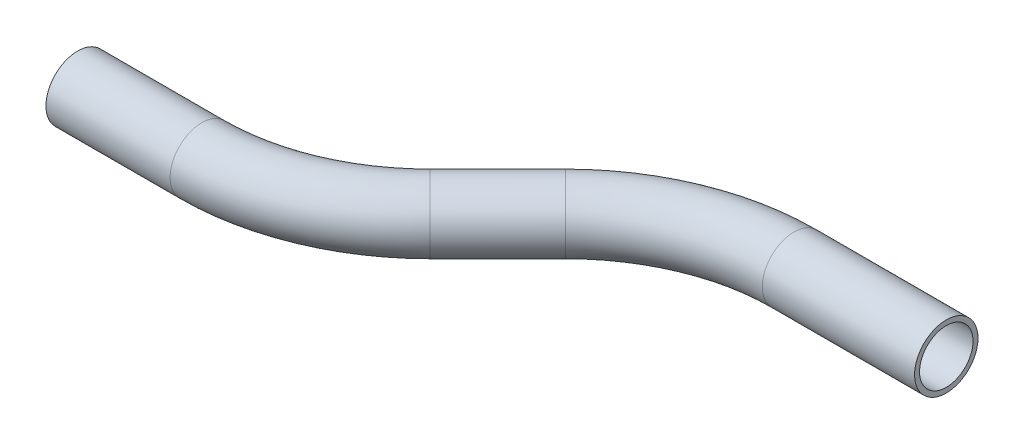
SolidWorks part; units mm, degrees
ref_plane "Front Plane" through (0, 0, 0) normal (0, 0, 1) x (1, 0, 0)
ref_plane "Top Plane" through (0, 0, 0) normal (0, 1, 0) x (1, 0, 0)
ref_plane "Right Plane" through (0, 0, 0) normal (1, 0, 0) x (0, 0, -1)
sketch "Sketch1" plane through (0, 0, 0) normal (0, 1, 0) x (1, 0, 0)
  line L0 (0, 0) -> (31.0664, 0)
  line L1 (71.4775, 16.7388) -> (88.4159, 33.6773)
  line L2 (128.8271, 50.4161) -> (166.9271, 50.4161)
  arc A1 (88.4159, 33.6773) -> (128.8271, 50.4161) centre (128.8271, -6.7339) cw
  arc A2 (31.0664, 0) -> (71.4775, 16.7388) centre (31.0664, 57.15) ccw
  point P10 (105.1548, 50.4161)
  point P14 (54.7387, 0)
  dimension "D3" = 57.15
  dimension "D1" = 54.7387
  dimension "D2" = 38.1
  dimension "D4" = 45
  dimension "D5" = 50.4161
ref_plane "Plane1" through (0, 0, 0) normal (1, 0, 0) x (0, 0, -1)
sketch "Sketch2" plane through (0, 0, 0) normal (1, 0, 0) x (0, 0, -1)
  circle A0 centre (0, 0) radius 7.9375
  circle A1 centre (0, 0) radius 6.6929
  dimension "D1" = 15.875
  dimension "D2" = 1.2446
sweep "Sweep1" add profiles "Sketch2" path "Sketch1"
